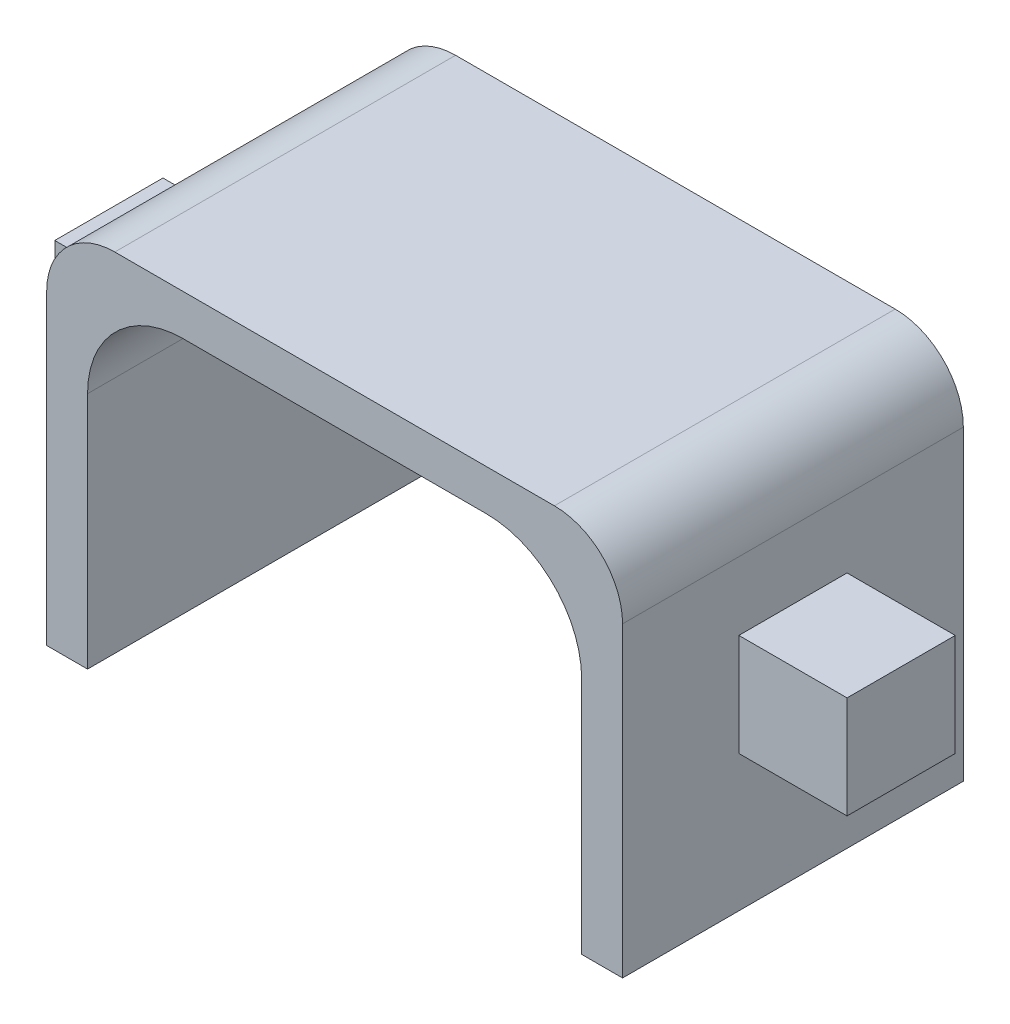
SolidWorks part; units mm, degrees
ref_plane "Front Plane" through (0, 0, 0) normal (0, 0, 1) x (1, 0, 0)
ref_plane "Top Plane" through (0, 0, 0) normal (0, 1, 0) x (1, 0, 0)
ref_plane "Right Plane" through (0, 0, 0) normal (1, 0, 0) x (0, 0, -1)
sketch "Sketch1" plane through (0, 0, 0) normal (0, 0, 1) x (1, 0, 0)
  line L0 (8.45, 11) -> (8.45, 7)
  line L1 (-8.45, 0) -> (8.45, 0) construction
  line L2 (0, 0) -> (0, 11) construction
  line L3 (-8.45, 11) -> (8.45, 11)
  line L4 (8.45, 0) -> (8.45, 11) construction
  line L5 (8.45, 4) -> (11.625, 4)
  line L6 (6.45, 9) -> (6.45, 0)
  line L7 (6.45, 0) -> (8.45, 0)
  line L8 (11.625, 4) -> (11.625, 7)
  line L9 (8.45, 5.5) -> (11.625, 7) construction
  line L10 (8.45, 5.5) -> (11.625, 4) construction
  line L11 (8.45, 4) -> (8.45, 0)
  line L12 (-8.45, 5.5) -> (-11.625, 4) construction
  line L13 (6.45, 9) -> (-6.45, 9)
  line L14 (8.45, 7) -> (11.625, 7)
  line L15 (-8.45, 5.5) -> (-11.625, 7) construction
  line L16 (-8.45, 0) -> (-8.45, 11) construction
  line L17 (-8.45, 7) -> (-11.625, 7)
  line L18 (-8.45, 4) -> (-8.45, 0)
  line L19 (-11.625, 4) -> (-11.625, 7)
  line L20 (-6.45, 0) -> (-8.45, 0)
  line L21 (-6.45, 9) -> (-6.45, 0)
  line L22 (-8.45, 4) -> (-11.625, 4)
  line L23 (-8.45, 11) -> (-8.45, 7)
  point P5 (8.45, 5.5)
  point P21 (0, 9)
  dimension "D1" = 11
  dimension "D2" = 8.45
  dimension "D3" = 3
  dimension "D4" = 3.175
  dimension "D6" = 2
extrude "Boss-Extrude1" add sketch "Sketch1" along normal mid plane 3.175
sketch "Sketch2" plane through (0, 0, 0) normal (0, 0, 1) x (1, 0, 0)
  line L0 (-8.45, 7) -> (-8.45, 4)
  line L1 (8.45, 7) -> (8.45, 4)
  line L16 (8.45, 11) -> (-8.45, 11)
  line L17 (-8.45, 11) -> (-8.45, 7)
  line L18 (-8.45, 7) -> (-11.625, 7)
  line L19 (-11.625, 7) -> (-11.625, 4)
  line L20 (-11.625, 4) -> (-8.45, 4)
  line L21 (-8.45, 4) -> (-8.45, 0)
  line L22 (-8.45, 0) -> (-6.45, 0)
  line L23 (-6.45, 0) -> (-6.45, 9)
  line L24 (-6.45, 9) -> (6.45, 9)
  line L25 (6.45, 9) -> (6.45, 0)
  line L26 (6.45, 0) -> (8.45, 0)
  line L27 (8.45, 0) -> (8.45, 4)
  line L28 (8.45, 4) -> (11.625, 4)
  line L29 (11.625, 4) -> (11.625, 7)
  line L30 (11.625, 7) -> (8.45, 7)
  line L31 (8.45, 7) -> (8.45, 11)
  line L32 (8.45, 11) -> (-8.45, 11)
  line L33 (-8.45, 11) -> (-8.45, 7)
  line L37 (-8.45, 4) -> (-8.45, 0)
  line L38 (-8.45, 0) -> (-6.45, 0)
  line L39 (-6.45, 0) -> (-6.45, 9)
  line L40 (-6.45, 9) -> (6.45, 9)
  line L41 (6.45, 9) -> (6.45, 0)
  line L42 (6.45, 0) -> (8.45, 0)
  line L43 (8.45, 0) -> (8.45, 4)
  line L47 (8.45, 7) -> (8.45, 11)
  dimension "D1" = 0
extrude "Boss-Extrude2" add sketch "Sketch2" along normal mid plane 10
fillet "Fillet1" radius 2 2 edges at (-6.45, 9, 0) (6.45, 9, 0)
fillet "Fillet2" radius 2 2 edges at (8.45, 11, 0) (-8.45, 11, 0)
sketch "Sketch3" plane through (0, 0, 5) normal (0, 0, 1) x (1, 0, 0)
  line L25 (-8.45, 0) -> (-6.45, 0) construction
  line L26 (6.45, 0) -> (8.45, 0) construction
  line L27 (6.45, 7) -> (6.45, 0) construction
  line L28 (7.25, 7) -> (7.25, 0)
  line L29 (-4.45, 9.8) -> (4.45, 9.8)
  line L30 (-7.25, 0) -> (-7.25, 7)
  line L31 (7.25, 7) -> (7.25, 0)
  line L32 (-4.45, 9.8) -> (4.45, 9.8)
  line L33 (-7.25, 0) -> (-7.25, 7)
  line L34 (-4.45, 9) -> (4.45, 9) construction
  line L35 (-6.45, 0) -> (-6.45, 7) construction
  line L36 (-7.25, 0) -> (-6.45, 0)
  line L37 (6.45, 0) -> (7.25, 0)
  line L38 (6.45, 7) -> (6.45, 0)
  line L39 (-4.45, 9) -> (4.45, 9)
  line L40 (-6.45, 0) -> (-6.45, 7)
  arc A14 (6.45, 7) -> (4.45, 9) centre (4.45, 7) ccw construction
  arc A15 (-4.45, 9) -> (-6.45, 7) centre (-4.45, 7) ccw construction
  arc A16 (7.25, 7) -> (4.45, 9.8) centre (4.45, 7) ccw
  arc A17 (-4.45, 9.8) -> (-7.25, 7) centre (-4.45, 7) ccw
  arc A18 (7.25, 7) -> (4.45, 9.8) centre (4.45, 7) ccw
  arc A19 (-4.45, 9.8) -> (-7.25, 7) centre (-4.45, 7) ccw
  arc A20 (6.45, 7) -> (4.45, 9) centre (4.45, 7) ccw
  arc A21 (-4.45, 9) -> (-6.45, 7) centre (-4.45, 7) ccw
  dimension "D1" = 0.8
extrude "Cut-Extrude1" cut sketch "Sketch3" against normal blind 10
